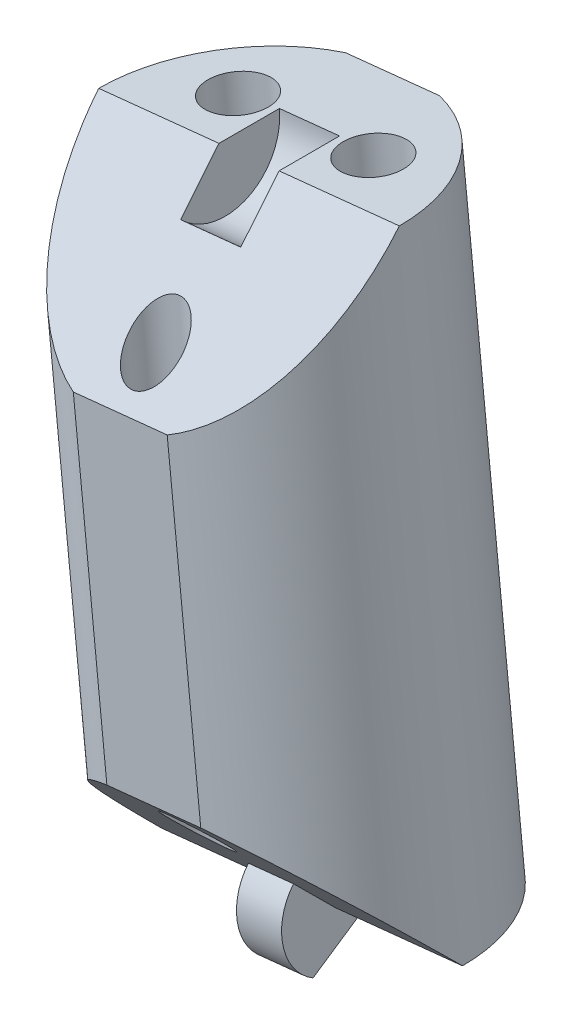
SolidWorks part; units mm, degrees
ref_plane "Front Plane" through (0, 0, 0) normal (0, 0, 1) x (1, 0, 0)
ref_plane "Top Plane" through (0, 0, 0) normal (0, 1, 0) x (1, 0, 0)
ref_plane "Right Plane" through (0, 0, 0) normal (1, 0, 0) x (0, 0, -1)
sketch "Sketch2" plane through (0, 0, 0) normal (0, 0, 1) x (1, 0, 0)
  line L0 (0, 0) -> (90, 0)
  line L1 (90, 0) -> (90, 120)
  line L2 (90, 120) -> (0, 120)
  line L3 (0, 120) -> (0, 0)
  line L4 (0, 120) -> (-10, 120)
  line L5 (-10, 120) -> (-10, 16.9491)
  line L6 (-10, 120) -> (57.5, 127)
  line L7 (57.5, 127) -> (90, 124)
  line L8 (90, 120) -> (99, 60)
  line L10 (90, 124) -> (90, 120)
  line L11 (5.9147, 0) -> (5.9147, -25)
  line L12 (5.9147, -25) -> (-4.0853, -25)
  line L13 (-4.0853, -29) -> (-4.0853, 0)
  line L14 (80, 0) -> (80, -25)
  line L15 (80, -25) -> (90, -25)
  line L16 (90, -29) -> (90, 0)
  line L17 (15.7927, 122.6748) -> (5.4776, 222.1414)
  line L18 (5.4776, 222.1414) -> (21.3923, 223.7918)
  line L19 (21.3923, 223.7918) -> (31.7073, 124.3252)
  line L20 (7.6492, 201.201) -> (23.5639, 202.8514)
  line L21 (10.9066, 169.7905) -> (26.8212, 171.441)
  line L22 (-10, 120) -> (-20.0396, 216.8108)
  line L23 (-20.0396, 216.8108) -> (-4.125, 218.4612)
  line L24 (-4.125, 218.4612) -> (5.9147, 121.6504)
  line L25 (-17.926, 196.4296) -> (-2.0114, 198.08)
  line L26 (-14.7556, 165.8578) -> (1.159, 167.5082)
  line L27 (57.5, 127) -> (46.9095, 229.1223)
  line L28 (46.9095, 229.1223) -> (30.9949, 227.4719)
  line L29 (30.9949, 227.4719) -> (41.5853, 125.3496)
  line L30 (33.2245, 205.9725) -> (49.1391, 207.6229)
  line L31 (36.5688, 173.7233) -> (52.4835, 175.3737)
  line L34 (90, 124) -> (99.1917, 223.5767)
  line L35 (99.1917, 223.5767) -> (83.2594, 225.0473)
  line L36 (83.2594, 225.0473) -> (74.0677, 125.4707)
  line L38 (81.3243, 204.0838) -> (97.2566, 202.6132)
  line L39 (78.4217, 172.6386) -> (94.354, 171.1679)
  line L40 (62.4078, 79.6749) -> (57.5, 127) construction
  line L41 (41.5853, 125.3496) -> (46.4931, 78.0244) construction
  line L42 (46.4931, 78.0244) -> (62.4078, 79.6749) construction
  line L43 (31.7073, 124.3252) -> (36.6151, 77.0001) construction
  line L44 (36.6151, 77.0001) -> (20.7005, 75.3496) construction
  line L45 (20.7005, 75.3496) -> (15.7927, 122.6748) construction
  line L46 (5.9147, 121.6504) -> (10.8224, 74.3253) construction
  line L47 (10.8224, 74.3253) -> (-5.0922, 72.6749) construction
  line L48 (-5.0922, 72.6749) -> (-10, 120) construction
  line L49 (74.0677, 125.4707) -> (69.6944, 78.0931) construction
  line L50 (69.6944, 78.0931) -> (85.7624, 78.0931) construction
  line L51 (85.7624, 78.0931) -> (90, 124) construction
  line L52 (-12.0823, 217.636) -> (10.4873, 0) construction
  line L53 (13.4349, 222.9666) -> (36.5574, 0) construction
  line L54 (38.9522, 228.2971) -> (62.6275, 0) construction
  line L55 (91.2256, 224.312) -> (70.5198, 0) construction
  line L59 (99, 60) -> (93.5277, 44.9649)
  line L60 (99, 60) -> (169.4769, 34.3485)
  line L61 (169.4769, 34.3485) -> (164.0046, 19.3134)
  line L62 (164.0046, 19.3134) -> (93.5277, 44.9649)
  line L63 (90, -2) -> (100, -2)
  line L64 (141.2862, 44.6091) -> (135.8138, 29.574)
  line L65 (99, 60) -> (55.7741, 75.7329) construction
  line L66 (55.7741, 75.7329) -> (50.3018, 60.6978) construction
  line L67 (100, -2) -> (100, -29)
  line L70 (-4.0853, -2) -> (-14.0853, -2)
  line L71 (-14.0853, -2) -> (-14.0853, -29)
  line L74 (-4.0853, 0) -> (0, 0)
  line L75 (-14.0853, -29) -> (-14.0853, -112.587)
  line L76 (-14.0853, -112.587) -> (100, -112.587)
  line L77 (100, -112.587) -> (100, -29)
  line L78 (-14.0853, -29) -> (100, -29)
  line L79 (-14.0853, -14.5) -> (100, -14.5) construction
  line L80 (31.7073, -112.587) -> (31.7073, -122.6232)
  line L81 (31.7073, -122.6232) -> (42.9573, -122.6232)
  line L82 (42.9573, -122.6232) -> (42.9573, -112.587)
  line L83 (-14.0853, -112.587) -> (-88.3667, -112.587)
  line L84 (-88.3667, -112.587) -> (-88.3667, -128.2699)
  line L85 (-88.3667, -128.2699) -> (169.4958, -128.2699)
  line L86 (169.4958, -128.2699) -> (169.4958, -112.587)
  line L87 (169.4958, -112.587) -> (100, -112.587)
  line L88 (90, 60) -> (-10, 60) construction
  line L89 (50.3018, 60.6978) -> (93.5277, 44.9649) construction
  line L90 (87.2806, 55.7521) -> (166.7408, 26.8309) construction
  line L91 (87.2806, 55.7521) -> (82.1749, 52.5336) construction
  line L92 (82.1749, 52.5336) -> (77.3257, 0) construction
  line L93 (83.1185, 56.6957) -> (86.337, 51.59) construction
  arc A0 (-10, 16.9491) -> (-4.0853, 0) centre (14.9876, 16.1624) ccw
  arc A1 (93.5277, 44.9649) -> (90, 0) centre (-126.4069, 39.5988) cw
  point P42 (41.1818, 206.7977)
  point P100 (84.7278, 54.1428)
  point P101 (84.7278, 54.1428)
  dimension "D11" = 47.3684
  dimension "D35" = 9
  dimension "D32" = 220
  dimension "D36" = 25
  dimension "D1" = 120
  dimension "D2" = 90
  dimension "D3" = 10
  dimension "D5" = 67.862
  dimension "D6" = 7
  dimension "D7" = 4
  dimension "D8" = 16
  dimension "D9" = 16
  dimension "D10" = 100
  dimension "D12" = 31.5789
  dimension "D13" = 16
  dimension "D14" = 16
  dimension "D15" = 16
  dimension "D16" = 25.7927
  dimension "D17" = 100
  dimension "D18" = 21.0526
  dimension "D19" = 31.5789
  dimension "D20" = 97.33
  dimension "D21" = 102.67
  dimension "D22" = 20.4905
  dimension "D23" = 30.7358
  dimension "D24" = 21.6147
  dimension "D25" = 32.4221
  dimension "D26" = 25
  dimension "D28" = 25
  dimension "D29" = 75
  dimension "D30" = 47.5789
  dimension "D31" = 30
  dimension "D33" = 46
  dimension "D34" = 20
  dimension "D37" = 2
  dimension "D38" = 2
  dimension "D39" = 27
  dimension "D40" = 10
  dimension "D41" = 10
  dimension "D42" = 27
  dimension "D43" = 14.5
  dimension "D44" = 127.5
ref_plane "Plane1" through (87.2806, 55.7521, 0) normal (-0.846, -0.5333, 0) x (0, 0, 1)
ref_plane "Plane2" through (82.1749, 52.5336, 0) normal (-0.0919, -0.9958, 0) x (-0.9958, 0.0919, 0)
ref_plane "Plane3" through (91.2256, 224.312, 0) normal (-0.0919, -0.9958, 0) x (-0.9958, 0.0919, 0)
ref_plane "Plane4" through (38.9522, 228.2971, 0) normal (0.1032, -0.9947, 0) x (-0.9947, -0.1032, 0)
ref_plane "Plane5" through (13.4349, 222.9666, 0) normal (0.1032, -0.9947, 0) x (-0.9947, -0.1032, 0)
ref_plane "Plane7" through (166.7408, 26.8309, 0) normal (0.9397, -0.342, 0) x (0, 0, -1)
ref_plane "Plane8" through (110.4217, -40.1902, 0) normal (0.9397, -0.342, 0) x (0, 0, -1)
ref_plane "Plane9" through (19.3664, 209.803, 0) normal (-0.0919, -0.9958, 0) x (-0.9958, 0.0919, 0)
ref_plane "Plane10" through (16.4638, 178.3578, 0) normal (-0.0919, -0.9958, 0) x (-0.9958, 0.0919, 0)
ref_plane "Plane11" through (-20.7793, 200.3721, 0) normal (0.1032, -0.9947, 0) x (-0.9947, -0.1032, 0)
ref_plane "Plane12" through (-17.435, 168.1229, 0) normal (0.1032, -0.9947, 0) x (-0.9947, -0.1032, 0)
ref_plane "Plane13" through (-20.5619, 198.2754, 0) normal (0.1032, -0.9947, 0) x (-0.9947, -0.1032, 0)
ref_plane "Plane14" through (-17.3045, 166.8649, 0) normal (0.1032, -0.9947, 0) x (-0.9947, -0.1032, 0)
ref_plane "Plane15" through (-12.0823, 217.636, 0) normal (0.1032, -0.9947, 0) x (-0.9947, -0.1032, 0)
ref_plane "Plane16" through (-20.3445, 196.1788, 0) normal (0.1032, -0.9947, 0) x (-0.9947, -0.1032, 0)
ref_plane "Plane17" through (-17.1741, 165.607, 0) normal (0.1032, -0.9947, 0) x (-0.9947, -0.1032, 0)
ref_plane "Plane18" through (12.1098, 131.1899, 0) normal (-0.0919, -0.9958, 0) x (-0.9958, 0.0919, 0)
ref_plane "Plane19" through (-12.4184, 119.7492, 0) normal (0.1032, -0.9947, 0) x (-0.9947, -0.1032, 0)
ref_plane "Plane20" through (0, 0, 0) normal (0, 0, 1) x (0.1032, -0.9947, 0)
ref_plane "Plane21" through (0, 0, 0) normal (0, 0, 1) x (-0.0919, -0.9958, 0)
ref_plane "Plane22" through (10.3758, 1.076, 0) normal (-0.9947, -0.1032, 0) x (0.1032, -0.9947, 0)
ref_plane "Plane23" through (36.1684, 3.7508, 0) normal (-0.9947, -0.1032, 0) x (0.1032, -0.9947, 0)
ref_plane "Plane24" through (61.9611, 6.4256, 0) normal (-0.9947, -0.1032, 0) x (0.1032, -0.9947, 0)
ref_plane "Plane25" through (69.924, -6.4545, 0) normal (-0.9958, 0.0919, 0) x (-0.0919, -0.9958, 0)
sketch "Sketch3" plane through (-20.3445, 196.1788, 0) normal (0.1032, -0.9947, 0) x (-0.9947, -0.1032, 0)
  line L0 (-2.4314, 0) -> (-18.4314, 0) construction
  circle A0 centre (-10.4314, 0) radius 8
  dimension "D1" = 16
extrude "Boss-Extrude1" add sketch "Sketch3" along normal blind 32.4221
sketch "Sketch4" plane through (10.3758, 1.076, 0) normal (-0.9947, -0.1032, 0) x (0.1032, -0.9947, 0)
  line L0 (-197.2309, 0) -> (-189.2309, 8)
  line L1 (-197.2309, 8) -> (-197.2309, -8) construction
  line L2 (-164.8088, 8) -> (-197.2309, 8) construction
  line L3 (-189.2309, 8) -> (-197.2309, 8)
  line L4 (-197.2309, 8) -> (-197.2309, 0)
  line L5 (-172.8088, 8) -> (-164.8088, 8)
  line L6 (-164.8088, 8) -> (-164.8088, 0)
  line L7 (-217.7214, 0) -> (1.0818, 0) construction
  line L8 (-164.8088, 0) -> (-172.8088, 8)
  dimension "D1" = 45
  dimension "D2" = 45
extrude "Cut-Extrude1" cut sketch "Sketch4" against normal through all and the other way through all
sketch "Sketch5" plane through (10.3758, 1.076, 0) normal (-0.9947, -0.1032, 0) x (0.1032, -0.9947, 0)
  line L1 (-164.8088, -2.8) -> (-162.3839, 1.4)
  line L6 (-164.8088, 0) -> (-172.8088, 8) construction
  line L11 (-164.8088, -8) -> (-164.8088, 0) construction
  line L12 (-166.7887, 1.9799) -> (-164.8088, 0)
  line L13 (-164.8088, 0) -> (-164.8088, -2.8)
  arc A3 (-166.7887, 1.9799) -> (-162.3839, 1.4) centre (-164.8088, 0) cw
  dimension "D2" = 2.8
  dimension "D1" = 30
  dimension "D3" = 2.8
extrude "Boss-Extrude2" add sketch "Sketch5" along normal mid plane 2.4
sketch "Sketch7" plane through (10.3758, 1.076, 0) normal (-0.9947, -0.1032, 0) x (0.1032, -0.9947, 0)
  line L6 (-197.2309, 0) -> (-197.2309, -8) construction
  line L7 (-189.2309, 8) -> (-197.2309, 0) construction
  line L8 (-194.9681, 2.2627) -> (-197.2309, 0)
  line L9 (-197.2309, 0) -> (-197.2309, -3.2)
  arc A1 (-197.2309, -3.2) -> (-194.9681, 2.2627) centre (-197.2309, 0) ccw
  dimension "D1" = 3.2
extrude "Cut-Extrude2" cut sketch "Sketch7" against normal mid plane 3.2
sketch "Sketch8" plane through (-20.3445, 196.1788, 0) normal (-0.1032, 0.9947, 0) x (0.9947, 0.1032, 0)
  line L0 (2.4314, 0) -> (18.4314, 0) construction
  circle A0 centre (10.4314, -5.5) radius 1.4
  circle A1 centre (6.8314, 3) radius 1.6
  circle A2 centre (14.0314, 3) radius 1.6
  point P9 (10.4314, 0)
  dimension "D1" = 3.2
  dimension "D2" = 3.2
  dimension "D3" = 2.8
  dimension "D4" = 3
  dimension "D5" = 5.5
  dimension "D6" = 3.6
  dimension "D7" = 3.6
  dimension "D8" = 3
extrude "Cut-Extrude3" cut sketch "Sketch8" against normal through all and the other way through all
sketch "Sketch9" plane through (-20.3445, 196.1788, 0) normal (-0.1032, 0.9947, 0) x (0.9947, 0.1032, 0)
  line L0 (7.9334, 7.6) -> (12.9294, 7.6)
  line L1 (-101.1265, 0) -> (155.3606, 0) construction
  line L2 (7.9334, -7.6) -> (12.9294, -7.6)
  arc A0 (18.4314, 0) -> (2.4314, 0) centre (10.4314, 0) ccw construction
  arc A1 (7.9334, 7.6) -> (12.9294, 7.6) centre (10.4314, 0) cw
  arc A2 (2.4314, 0) -> (18.4314, 0) centre (10.4314, 0) ccw construction
  arc A3 (7.9334, -7.6) -> (12.9294, -7.6) centre (10.4314, 0) ccw
  dimension "D1" = 7.6
  dimension "D2" = 7.6
extrude "Cut-Extrude4" cut sketch "Sketch9" against normal through all
